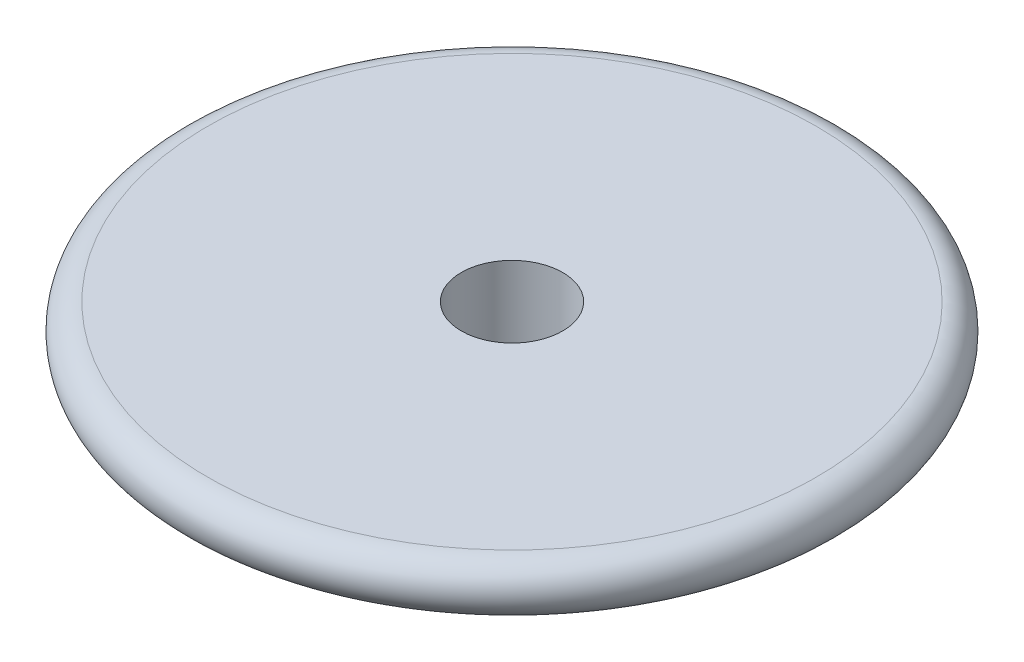
SolidWorks part; units mm, degrees
ref_plane "Front Plane" through (0, 0, 0) normal (0, 0, 1) x (1, 0, 0)
ref_plane "Top Plane" through (0, 0, 0) normal (0, 1, 0) x (1, 0, 0)
ref_plane "Right Plane" through (0, 0, 0) normal (1, 0, 0) x (0, 0, -1)
sketch "Sketch1" plane through (0, 0, 0) normal (1, 0, 0) x (0, 0, -1)
  line L0 (0, 0) -> (-12, 0)
  line L1 (0, -4) -> (0, 0)
  line L2 (1.2608, -4) -> (0, -4)
  arc A0 (-12, 0) -> (-12.3243, -1.9459) centre (-12, -1) ccw
  arc A1 (-12.3243, -1.9459) -> (0, -4) centre (0, 34) ccw
  dimension "D1" = 1
  dimension "D2" = 13
  dimension "D3" = 4
revolve "Revolve1" add sketch "Sketch1" angle 360 about L1
sketch "Sketch2" plane through (0, 0, 0) normal (0, 1, 0) x (1, 0, 0)
  circle A0 centre (0, 0) radius 2
  dimension "D1" = 4
extrude "Cut-Extrude1" cut sketch "Sketch2" against normal through all
